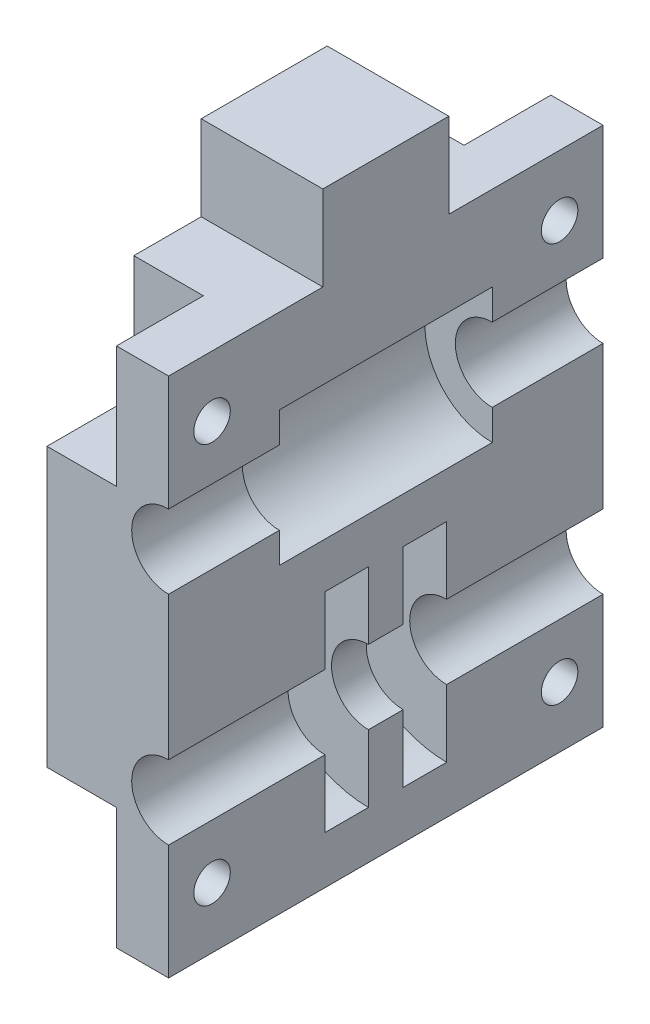
SolidWorks part; units mm, degrees
ref_plane "Front Plane" through (0, 0, 0) normal (0, 0, 1) x (1, 0, 0)
ref_plane "Top Plane" through (0, 0, 0) normal (0, 1, 0) x (1, 0, 0)
ref_plane "Right Plane" through (0, 0, 0) normal (1, 0, 0) x (0, 0, -1)
sketch "Sketch1" plane through (0, 0, 0) normal (0, 0, 1) x (1, 0, 0)
  line L0 (7, 0) -> (23.8395, 0) construction
  line L1 (-7, 30) -> (7, 30)
  line L2 (-7, 30) -> (-7, -30)
  line L3 (-7, -30) -> (7, -30)
  line L4 (7, 30) -> (7, 16.75)
  line L5 (-7, 30) -> (7, -30) construction
  line L6 (-7, -30) -> (7, 30) construction
  line L7 (7, 8.25) -> (7, -8.25)
  line L8 (7, -16.75) -> (7, -30)
  arc A0 (7, 16.75) -> (7, 8.25) centre (7, 12.5) ccw
  arc A1 (7, -16.75) -> (7, -8.25) centre (7, -12.5) cw
  point P0 (0, 0)
  dimension "D3" = 12.5
  dimension "D4" = 8.5
  dimension "D1" = 14
  dimension "D2" = 60
extrude "Boss-Extrude1" add sketch "Sketch1" along normal blind 50
ref_plane "Plane1" through (0, 0, 25) normal (0, 0, -1) x (-1, 0, 0)
sketch "Sketch2" plane through (0, 0, 25) normal (0, 0, -1) x (-1, 0, 0)
  circle A0 centre (-7, 12.5) radius 7.75
  dimension "D1" = 15.5
extrude "Cut-Extrude1" cut sketch "Sketch2" against normal mid plane 24.5
ref_plane "Plane2" through (0, 0, 23) normal (0, 0, -1) x (-1, 0, 0)
sketch "Sketch4" plane through (0, 0, 23) normal (0, 0, -1) x (-1, 0, 0)
  circle A0 centre (-7, -12.5) radius 12
  dimension "D1" = 24
extrude "Cut-Extrude2" cut sketch "Sketch4" along normal blind 5
mirror "Mirror1" about plane through (0, 0, 25) normal (0, 0, -1) of "Cut-Extrude2"
sketch "Sketch5" plane through (-7, 0, 0) normal (-1, 0, 0) x (0, 0, 1)
  line L1 (0, 30) -> (10, 30)
  line L2 (0, 30) -> (0, 16)
  line L3 (0, 16) -> (10, 16)
  line L4 (10, 30) -> (10, 16)
  line L5 (0, 30) -> (10, 16) construction
  line L6 (0, 16) -> (10, 30) construction
  line L7 (50, 30) -> (40, 30)
  line L8 (50, 30) -> (50, 16)
  line L9 (50, 16) -> (40, 16)
  line L10 (40, 30) -> (40, 16)
  line L11 (50, 30) -> (40, 16) construction
  line L12 (50, 16) -> (40, 30) construction
  line L13 (50, -30) -> (40, -30)
  line L14 (50, -30) -> (50, -16)
  line L15 (50, -16) -> (40, -16)
  line L16 (40, -30) -> (40, -16)
  line L17 (50, -30) -> (40, -16) construction
  line L18 (50, -16) -> (40, -30) construction
  line L19 (0, -30) -> (10, -30)
  line L20 (0, -30) -> (0, -16)
  line L21 (0, -16) -> (10, -16)
  line L22 (10, -30) -> (10, -16)
  line L23 (0, -30) -> (10, -16) construction
  line L24 (0, -16) -> (10, -30) construction
  point P4 (5, 23)
  point P10 (45, 23)
  point P16 (45, -23)
  point P22 (5, -23)
  dimension "D1" = 14
  dimension "D2" = 10
extrude "Cut-Extrude3" cut sketch "Sketch5" against normal blind 8
sketch "Sketch6" plane through (1, 0, 0) normal (-1, 0, 0) x (0, 0, 1)
  line L0 (0, 30) -> (10, 16) construction
  line L1 (40, 30) -> (50, 16) construction
  line L2 (50, 16) -> (50, -16) construction
  line L3 (50, -16) -> (40, -30) construction
  line L4 (40, -30) -> (10, -30) construction
  line L5 (10, -30) -> (0, -16) construction
  circle A0 centre (5, 23) radius 2.1
  circle A1 centre (45, 23) radius 2.1
  circle A2 centre (5, -23) radius 2.1
  circle A3 centre (45, -23) radius 2.1
  dimension "D1" = 4.2
extrude "Cut-Extrude4" cut sketch "Sketch6" against normal through all
sketch "Sketch7" plane through (0, 30, 0) normal (0, 1, 0) x (1, 0, 0)
  line L0 (7, -50) -> (7, 0) construction
  line L1 (-7, -17.75) -> (7, -17.75)
  line L2 (-7, -17.75) -> (-7, -32.25)
  line L3 (-7, -32.25) -> (7, -32.25)
  line L5 (-7, -17.75) -> (7, -25) construction
  line L6 (-7, -32.25) -> (7, -25) construction
  line L7 (7, -17.75) -> (7, -32.25)
  line L8 (-7, -40) -> (-7, -10) construction
  point P0 (7, -25)
  point P1 (0, 0)
  point P11 (0, 0)
  dimension "D1" = 14.5
  dimension "D2" = 14
extrude "Boss-Extrude2" add sketch "Sketch7" along normal blind 9.77
